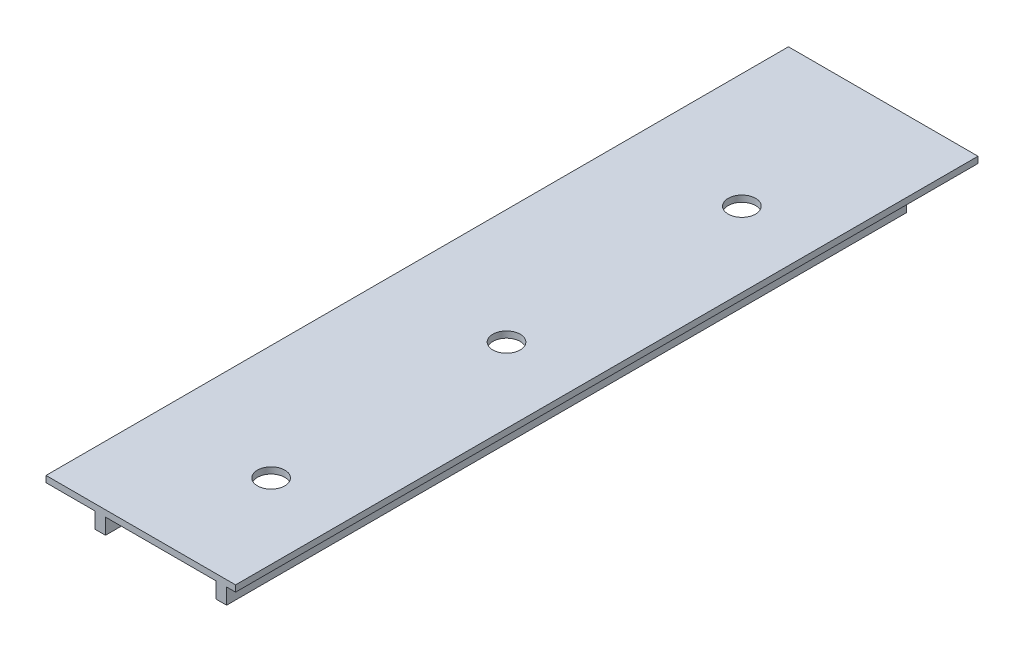
SolidWorks part; units mm, degrees
ref_plane "Front Plane" through (0, 0, 0) normal (0, 0, 1) x (1, 0, 0)
ref_plane "Top Plane" through (0, 0, 0) normal (0, 1, 0) x (1, 0, 0)
ref_plane "Right Plane" through (0, 0, 0) normal (1, 0, 0) x (0, 0, -1)
sketch "Sketch1" plane through (0, 0, 0) normal (0, 1, 0) x (1, 0, 0)
  line L1 (0, 0) -> (18, 0)
  line L2 (0, 0) -> (0, 70.5)
  line L3 (0, 70.5) -> (18, 70.5)
  line L4 (18, 0) -> (18, 70.5)
  dimension "D1" = 18
  dimension "D2" = 70.5
extrude "Boss-Extrude1" add sketch "Sketch1" along normal blind 0.6
ref_plane "Plane1" through (0, 0.3, 0) normal (0, 1, 0) x (1, 0, 0)
sketch "Sketch2" plane through (0, 0.3, 0) normal (0, 1, 0) x (1, 0, 0)
  line L1 (41.7314, -73.2431) -> (-41.7314, -73.2431)
  line L2 (41.7314, -73.2431) -> (41.7314, 73.2431)
  line L3 (41.7314, 73.2431) -> (-41.7314, 73.2431)
  line L4 (-41.7314, -73.2431) -> (-41.7314, 73.2431)
  line L5 (41.7314, -73.2431) -> (-41.7314, 73.2431) construction
  line L6 (41.7314, 73.2431) -> (-41.7314, -73.2431) construction
  point P0 (0, 0)
sketch "Sketch3" plane through (0, 0.6, 0) normal (0, 1, 0) x (1, 0, 0)
  line L0 (0, 0) -> (10.9, 0) construction
  line L1 (0, 0) -> (18, 0) construction
  line L2 (10.9, 0) -> (10.9, 10.48) construction
  line L3 (10.9, 10.48) -> (10.9, 32.83) construction
  line L4 (10.9, 32.83) -> (10.9, 55.18) construction
  circle A0 centre (10.9, 10.48) radius 1.3
  circle A1 centre (10.9, 32.83) radius 1.3
  circle A2 centre (10.9, 55.18) radius 1.3
  dimension "D1" = 2.6
  dimension "D3" = 2.6
  dimension "D5" = 2.6
  dimension "D2" = 22.35
  dimension "D4" = 22.35
  dimension "D6" = 10.48
extrude "Cut-Extrude1" cut sketch "Sketch3" against normal blind 10
sketch "Sketch4" plane through (0, 0, 0) normal (0, -1, 0) x (1, 0, 0)
  line L0 (18, 0) -> (10.9, -10.48) construction
  line L1 (10.9, -10.48) -> (10.9, 0) construction
  line L2 (0, 0) -> (18, 0) construction
  line L3 (10.9, 0) -> (10.9, -70.5) construction
  line L4 (18, -70.5) -> (0, -70.5) construction
  line L5 (10.9, 0) -> (16.65, 0) construction
  line L6 (5.15, 0) -> (4.65, 0)
  line L7 (16.65, 0) -> (16.15, 0)
  line L8 (16.65, 0) -> (16.65, -64.56)
  line L9 (16.65, -64.56) -> (16.15, -64.56)
  line L10 (16.15, 0) -> (16.15, -64.56)
  line L11 (16.65, -64.56) -> (17.15, -64.56)
  line L12 (16.65, -64.56) -> (16.65, 0)
  line L13 (16.65, 0) -> (17.15, 0)
  line L14 (17.15, -64.56) -> (17.15, 0)
  line L15 (4.65, -64.56) -> (4.65, 0)
  line L16 (5.15, -64.56) -> (4.65, -64.56)
  line L17 (5.15, -64.56) -> (5.15, 0)
  line L18 (5.15, -64.56) -> (5.65, -64.56)
  line L19 (5.65, 0) -> (5.65, -64.56)
  line L20 (5.15, 0) -> (5.65, 0)
  line L21 (5.15, 0) -> (5.15, -64.56)
  line M7 (18, 0) -> (0, 0)
  dimension "D1" = 5.75
  dimension "D2" = 0.5
  dimension "D3" = 0.5
  dimension "D4" = 64.56
extrude "Boss-Extrude2" add sketch "Sketch4" along normal blind 1.5 contours L11 L14 L8 M7 | L10 L9 L8 M7 | L19 L17 L18 M7 | L16 L17 L15 M7
